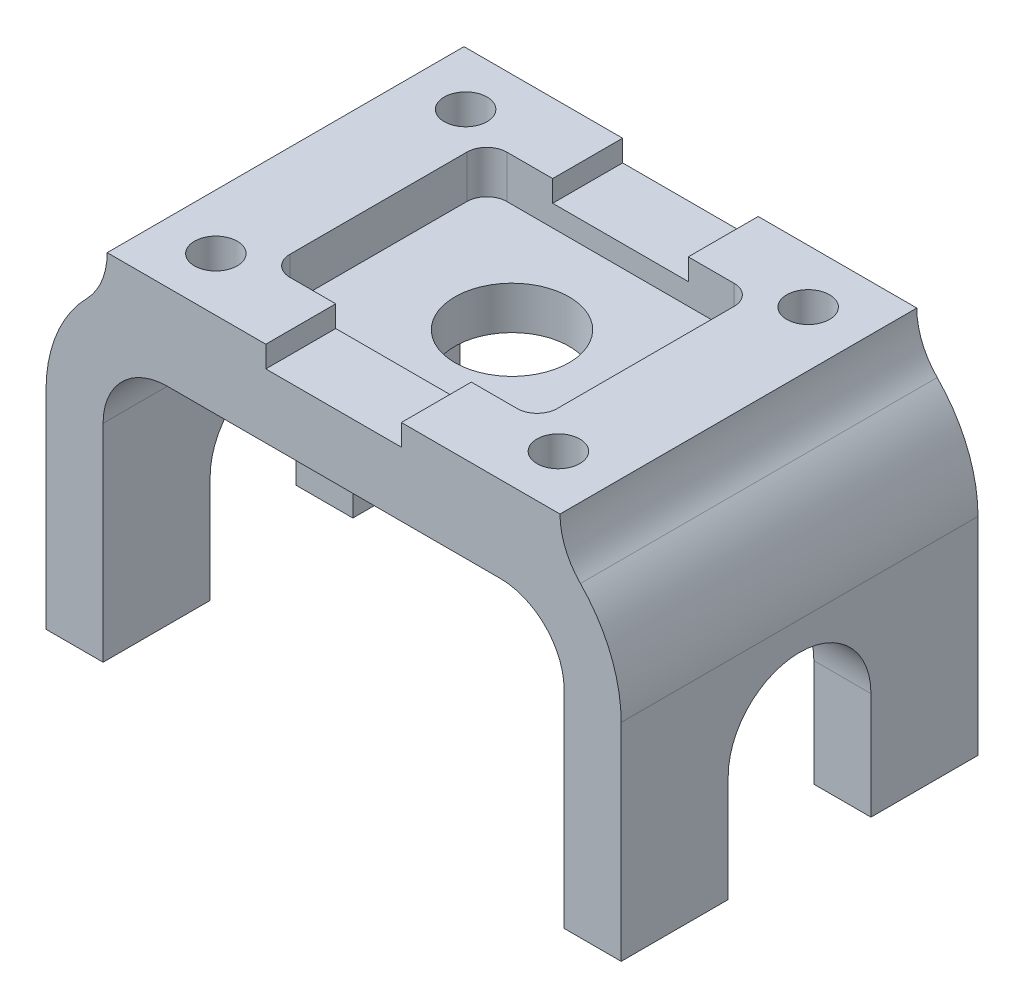
SolidWorks part; units mm, degrees
material "AISI 304"
ref_plane "Front Plane" through (0, 0, 0) normal (0, 0, 1) x (1, 0, 0)
ref_plane "Top Plane" through (0, 0, 0) normal (0, 1, 0) x (1, 0, 0)
ref_plane "Right Plane" through (0, 0, 0) normal (1, 0, 0) x (0, 0, -1)
sketch "Sketch2" plane through (0, 0, 0) normal (0, 0, 1) x (1, 0, 0)
  line L0 (-29.591, 0) -> (29.591, 0)
  line L1 (41.021, -11.43) -> (41.021, -48.26)
  line L2 (41.021, -48.26) -> (51.181, -48.26)
  line L3 (51.181, -48.26) -> (51.181, -11.43)
  line L4 (40.2898, 15.24) -> (-40.2898, 15.24)
  line L5 (-51.181, -11.43) -> (-51.181, -48.26)
  line L6 (-51.181, -48.26) -> (-41.021, -48.26)
  line L7 (-41.021, -48.26) -> (-41.021, -11.43)
  line L8 (0, 0) -> (0, 94.6407) construction
  arc A0 (51.181, -11.43) -> (43.9202, 6.35) centre (25.781, -11.43) ccw
  arc A1 (43.9202, 6.35) -> (40.2898, 15.24) centre (52.9898, 15.24) cw
  arc A2 (-40.2898, 15.24) -> (-43.9202, 6.35) centre (-52.9898, 15.24) cw
  arc A3 (-43.9202, 6.35) -> (-51.181, -11.43) centre (-25.781, -11.43) ccw
  arc A4 (29.591, 0) -> (41.021, -11.43) centre (29.591, -11.43) cw
  arc A5 (-29.591, 0) -> (-41.021, -11.43) centre (-29.591, -11.43) ccw
  dimension "D1" = 36.83
  dimension "D4" = 12.7
  dimension "D5" = 25.4
  dimension "D2" = 10.16
  dimension "D3" = 15.24
  dimension "D6" = 82.042
  dimension "D7" = 63.5
extrude "Boss-Extrude1" add sketch "Sketch2" along normal mid plane 63.5
sketch "Sketch3" plane through (51.181, 0, 0) normal (1, 0, 0) x (0, 0, -1)
  line L0 (-12.7, -48.26) -> (12.7, -48.26)
  line L1 (-31.75, -48.26) -> (31.75, -48.26) construction
  line L2 (12.7, -48.26) -> (12.7, -29.21)
  line L3 (-12.7, -29.21) -> (-12.7, -48.26)
  line L4 (0, -48.26) -> (0, 0) construction
  arc A0 (12.7, -29.21) -> (-12.7, -29.21) centre (0, -29.21) ccw
  dimension "D1" = 19.05
  dimension "Cut_Width" = 25.4
extrude "Cut-Extrude1" cut sketch "Sketch3" against normal through all
sketch "Sketch4" plane through (0, 15.24, 0) normal (0, 1, 0) x (1, 0, 0)
  line L0 (40.2898, 31.75) -> (-40.2898, 31.75) construction
  line L1 (-20.2238, 19.304) -> (20.2238, 19.304)
  line L2 (-23.7798, 15.748) -> (-23.7798, -15.748)
  line L3 (-20.2238, -19.304) -> (20.2238, -19.304)
  line L4 (23.7798, 15.748) -> (23.7798, -15.748)
  line L5 (-23.7798, -19.304) -> (23.7798, 19.304) construction
  line L6 (-40.2898, -31.75) -> (-40.2898, 31.75) construction
  arc A0 (-23.7798, -15.748) -> (-20.2238, -19.304) centre (-20.2238, -15.748) ccw
  arc A1 (20.2238, -19.304) -> (23.7798, -15.748) centre (20.2238, -15.748) ccw
  arc A2 (20.2238, 19.304) -> (23.7798, 15.748) centre (20.2238, 15.748) cw
  arc A3 (-20.2238, 19.304) -> (-23.7798, 15.748) centre (-20.2238, 15.748) ccw
  dimension "D3" = 3.556
  dimension "D1" = 12.446
  dimension "D2" = 16.51
extrude "Cut-Extrude2" cut sketch "Sketch4" against normal blind 7.62
sketch "Sketch5" plane through (0, 0, 31.75) normal (0, 0, 1) x (1, 0, 0)
  line L0 (0, 0) -> (0, 29.0489) construction
  line L1 (-29.591, 0) -> (29.591, 0) construction
  line L2 (40.2898, 15.24) -> (-40.2898, 15.24) construction
  line L3 (12.065, 15.24) -> (-12.065, 15.24)
  line L4 (12.065, 15.24) -> (12.065, 11.43)
  line L5 (12.065, 11.43) -> (-12.065, 11.43)
  line L6 (-12.065, 15.24) -> (-12.065, 11.43)
  dimension "D1" = 24.13
  dimension "D2" = 3.81
extrude "Cut-Extrude3" cut sketch "Sketch5" against normal through all
sketch "Sketch6" plane through (0, 7.62, 0) normal (0, 1, 0) x (1, 0, 0)
  circle A0 centre (0, 0) radius 10.16
  dimension "Hole_Diameter" = 20.32
extrude "Cut-Extrude4" cut sketch "Sketch6" against normal up to next
sketch "Sketch7" plane through (0, 15.24, 0) normal (0, 1, 0) x (1, 0, 0)
  line L0 (-57.8306, 0) -> (65.0092, 0) construction
  line L1 (0, -38.3252) -> (0, 42.5913) construction
  circle A0 centre (-30.48, 22.225) radius 3.81
  circle A1 centre (30.48, 22.225) radius 3.81
  circle A2 centre (30.48, -22.225) radius 3.81
  circle A3 centre (-30.48, -22.225) radius 3.81
  dimension "D1" = 7.62
  dimension "D2" = 60.96
  dimension "D3" = 44.45
extrude "Cut-Extrude5" cut sketch "Sketch7" against normal up to next
sketch "Sketch8" [suppressed] plane through (0, 7.62, 0) normal (0, 1, 0) x (1, 0, 0)
  line L0 (12.065, 38.354) -> (-12.065, 38.354) construction
  line L1 (-11.0798, -25.654) -> (11.0798, -25.654)
  line L2 (-11.0798, -25.654) -> (-11.0798, 25.654)
  line L3 (-11.0798, 25.654) -> (11.0798, 25.654)
  line L4 (11.0798, -25.654) -> (11.0798, 25.654)
  line L5 (-11.0798, -25.654) -> (11.0798, 25.654) construction
  line L6 (-11.0798, 25.654) -> (11.0798, -25.654) construction
  line L7 (23.7798, -34.798) -> (23.7798, 34.798) construction
  point P0 (0, 0)
  dimension "D1" = 12.7
  dimension "D2" = 12.7
extrude "Cut-Extrude6" [suppressed] cut sketch "Sketch8" against normal up to next
